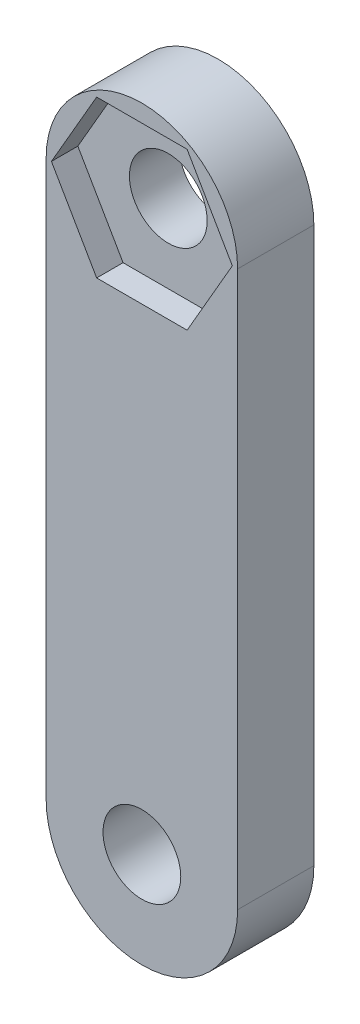
SolidWorks part; units mm, degrees
other "Markup1"
sketch "Sketch3" plane through (-7.9756, 31.0896, 6.35) normal (-0.7816, 0.3422, 0.5216) x (-0.4803, -0.8636, -0.1532)
ref_plane "Front Plane" through (0, 0, 0) normal (0, 0, 1) x (1, 0, 0)
ref_plane "Top Plane" through (0, 0, 0) normal (0, 1, 0) x (1, 0, 0)
ref_plane "Right Plane" through (0, 0, 0) normal (1, 0, 0) x (0, 0, -1)
sketch "Sketch1" plane through (0, 0, 0) normal (0, 0, 1) x (1, 0, 0)
  line L0 (0, 23.114) -> (0, -23.114) construction
  line L1 (7.9756, 23.114) -> (7.9756, -23.114)
  line L2 (-7.9756, 23.114) -> (-7.9756, -23.114)
  arc A0 (7.9756, 23.114) -> (-7.9756, 23.114) centre (0, 23.114) ccw
  arc A1 (-7.9756, -23.114) -> (7.9756, -23.114) centre (0, -23.114) ccw
  circle A2 centre (0, 23.114) radius 3.2385
  circle A3 centre (0, -23.114) radius 3.2385
  point P3 (0, 0)
  dimension "D1" = 6.477
  dimension "D2" = 6.477
  dimension "D3" = 46.228
  dimension "D4" = 15.9512
extrude "Boss-Extrude1" add sketch "Sketch1" along normal blind 6.35
sketch "Sketch2" plane through (0, 0, 6.35) normal (0, 0, 1) x (1, 0, 0)
  line L0 (-7.9756, 23.114) -> (-7.9756, -23.114) construction
  line L1 (-7.5344, 23.114) -> (-3.7672, 16.589)
  line L2 (-3.7672, 16.589) -> (3.7672, 16.589)
  line L3 (3.7672, 16.589) -> (7.5344, 23.114)
  line L4 (7.5344, 23.114) -> (3.7672, 29.639)
  line L5 (3.7672, 29.639) -> (-3.7672, 29.639)
  line L6 (-3.7672, 29.639) -> (-7.5344, 23.114)
  circle A0 centre (0, 23.114) radius 6.525 construction
  dimension "D1" = 13.05
extrude "Cut-Extrude1" cut sketch "Sketch2" against normal blind 2.2
sketch "Sketch4" plane through (0, 0, 4.15) normal (0, 0, 1) x (1, 0, 0)
  circle A0 centre (0, 23.114) radius 3
  circle A1 centre (0, 23.114) radius 3.2385 construction
  circle A2 centre (0, 23.114) radius 3.2385
  dimension "D1" = 6
sketch "Sketch5" plane through (0, 0, 6.35) normal (0, 0, 1) x (1, 0, 0)
  circle A0 centre (0, 23.114) radius 3.2385 construction
  circle A1 centre (0, 23.114) radius 3.2385
  circle A2 centre (0, 23.114) radius 9.9756
  arc A3 (7.9756, 23.114) -> (-7.9756, 23.114) centre (0, 23.114) ccw construction
  dimension "D1" = 2
